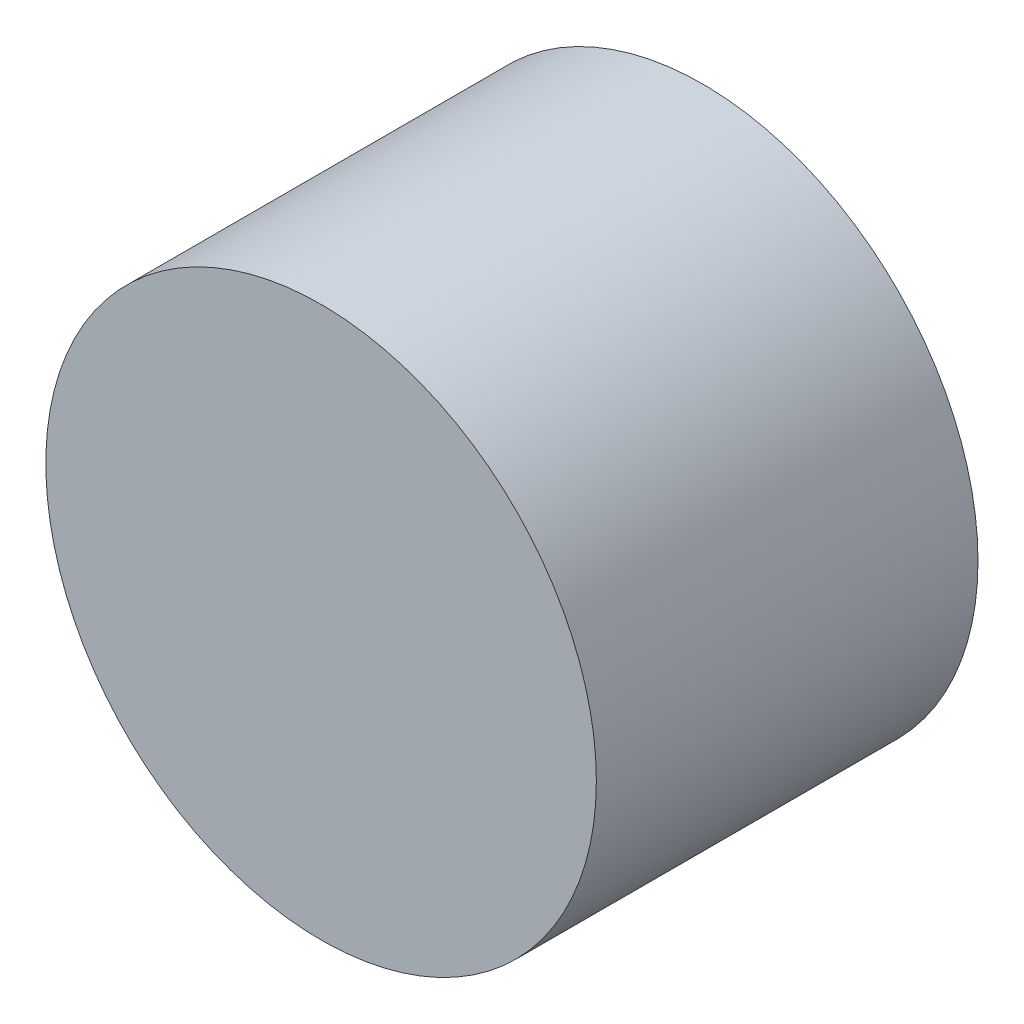
SolidWorks part; units mm, degrees
ref_plane "Plan de face" through (0, 0, 0) normal (0, 0, 1) x (1, 0, 0)
ref_plane "Plan de dessus" through (0, 0, 0) normal (0, 1, 0) x (1, 0, 0)
ref_plane "Plan de droite" through (0, 0, 0) normal (1, 0, 0) x (0, 0, -1)
sketch "Esquisse1" plane through (0, 0, 0) normal (0, 0, 1) x (1, 0, 0)
  circle A0 centre (0, 0) radius 75.7323
extrude "Boss.-Extru.1" add sketch "Esquisse1" along normal blind 100 and the other way blind 5
hole_wizard "Trou taraudé M8x1.01" positions "Esquisse6" profile "Esquisse5" tap size "M8x1.0" standard "Ansi Metric"
sketch "Esquisse6" plane through (0, 0, -5) normal (0, 0, -1) x (-1, 0, 0)
  point P0 (0, 0)
sketch "Esquisse5" plane through (0, 0, -5) normal (1, 0, 0) x (0, 1, 0)
  line L0 (0, 0) -> (0, 52.103)
  line L1 (0, 52.103) -> (3.5, 50)
  line L2 (3.5, 50) -> (3.5, 0)
  line L5 (3.5, 0) -> (0, 0)
  line L10 (0, 52.103) -> (-3.5, 50) construction
  line L11 (0, -6.35) -> (0, 107.95) construction
  dimension "Diamètre du trou pour taraudage" = 7
  dimension "Profondeur du trou pour taraudage" = 50
  dimension "Angle de pointe" = 118
cosmetic thread "Filetage de perçage1" parameters "D1"=45, "D2"=8
